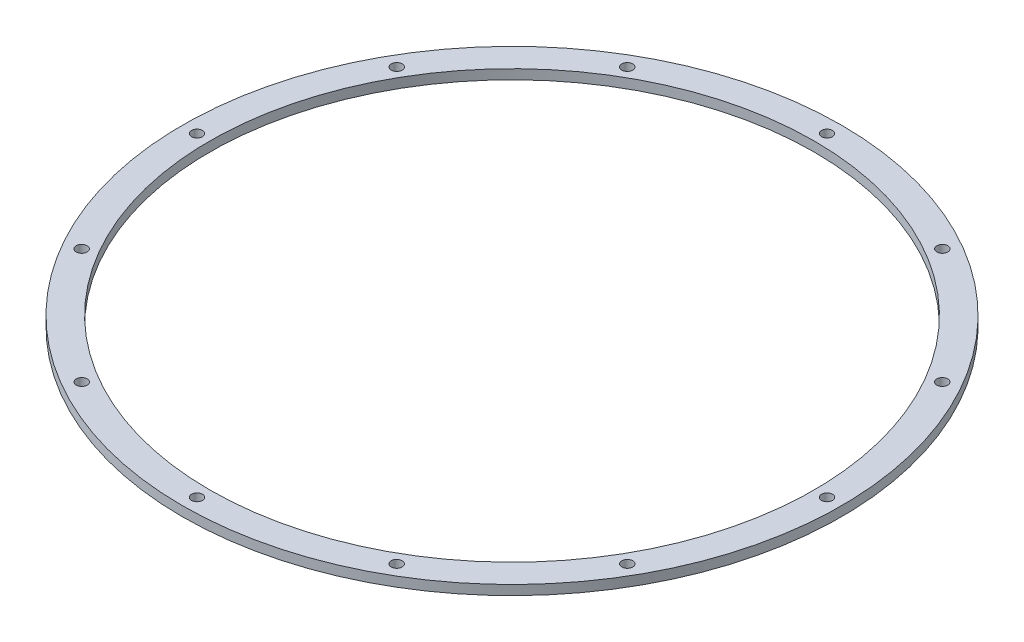
SolidWorks part; units mm, degrees
ref_plane "Front Plane" through (0, 0, 0) normal (0, 0, 1) x (1, 0, 0)
ref_plane "Top Plane" through (0, 0, 0) normal (0, 1, 0) x (1, 0, 0)
ref_plane "Right Plane" through (0, 0, 0) normal (1, 0, 0) x (0, 0, -1)
sketch "Sketch1" plane through (0, 0, 0) normal (0, 1, 0) x (1, 0, 0)
  circle A0 centre (0, 0) radius 94
  circle A1 centre (0, 0) radius 102.5
  circle A2 centre (0, 0) radius 97.974 construction
  circle A3 centre (0, 97.974) radius 1.7
  circle A4 centre (48.987, 84.848) radius 1.7
  circle A5 centre (84.848, 48.987) radius 1.7
  circle A6 centre (97.974, 0) radius 1.7
  circle A7 centre (84.848, -48.987) radius 1.7
  circle A8 centre (48.987, -84.848) radius 1.7
  circle A9 centre (0, -97.974) radius 1.7
  circle A10 centre (-48.987, -84.848) radius 1.7
  circle A11 centre (-84.848, -48.987) radius 1.7
  circle A12 centre (-97.974, 0) radius 1.7
  circle A13 centre (-84.848, 48.987) radius 1.7
  circle A14 centre (-48.987, 84.848) radius 1.7
  dimension "D1" = 188
  dimension "D2" = 205
  dimension "D3" = 195.948
  dimension "D4" = 3.4
  dimension "D5" = 12
extrude "Boss-Extrude1" add sketch "Sketch1" along normal blind 3 contours A1 A0
